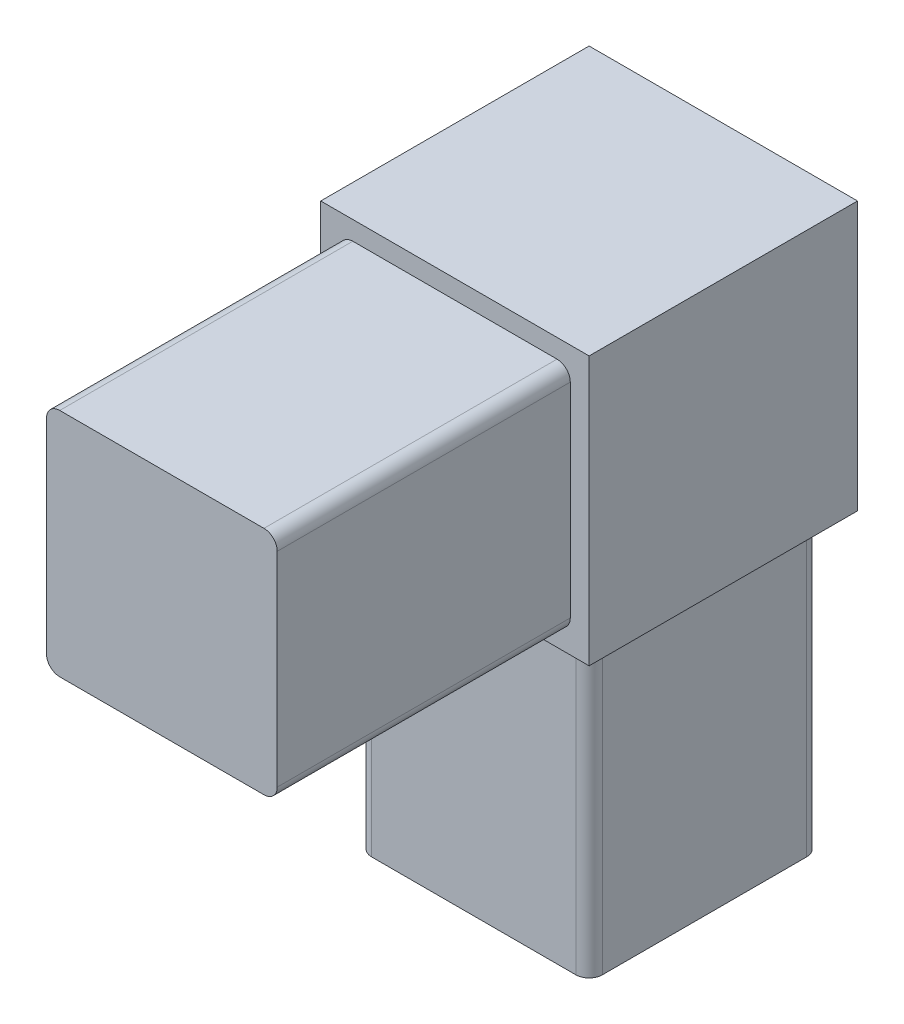
SolidWorks part; units mm, degrees
ref_plane "Front Plane" through (0, 0, 0) normal (0, 0, 1) x (1, 0, 0)
ref_plane "Top Plane" through (0, 0, 0) normal (0, 1, 0) x (1, 0, 0)
ref_plane "Right Plane" through (0, 0, 0) normal (1, 0, 0) x (0, 0, -1)
sketch "Sketch1" plane through (0, 0, 0) normal (0, 1, 0) x (1, 0, 0)
  line L1 (-11.049, 11.049) -> (11.049, 11.049)
  line L2 (-11.049, 11.049) -> (-11.049, -11.049)
  line L3 (-11.049, -11.049) -> (11.049, -11.049)
  line L4 (11.049, 11.049) -> (11.049, -11.049)
  line L5 (-11.049, 11.049) -> (11.049, -11.049) construction
  line L6 (-11.049, -11.049) -> (11.049, 11.049) construction
  point P0 (0, 0)
  dimension "D1" = 22.098
extrude "Boss-Extrude1" add sketch "Sketch1" along normal blind 28.067
sketch "Sketch2" plane through (0, 28.067, 0) normal (0, 1, 0) x (1, 0, 0)
  line L1 (-12.8524, -12.8524) -> (12.8524, -12.8524)
  line L2 (-12.8524, -12.8524) -> (-12.8524, 12.8524)
  line L3 (-12.8524, 12.8524) -> (12.8524, 12.8524)
  line L4 (12.8524, -12.8524) -> (12.8524, 12.8524)
  line L5 (-12.8524, -12.8524) -> (12.8524, 12.8524) construction
  line L6 (-12.8524, 12.8524) -> (12.8524, -12.8524) construction
  point P0 (0, 0)
  dimension "D1" = 25.7048
  dimension "D2" = 25.7048
extrude "Boss-Extrude2" add sketch "Sketch2" along normal blind 25.7048
sketch "Sketch3" plane through (0, 0, 12.8524) normal (0, 0, 1) x (1, 0, 0)
  line L0 (-12.8524, 53.7718) -> (12.8524, 28.067) construction
  line L2 (-11.049, 29.8704) -> (11.049, 29.8704)
  line L3 (-11.049, 29.8704) -> (-11.049, 51.9684)
  line L4 (-11.049, 51.9684) -> (11.049, 51.9684)
  line L5 (11.049, 29.8704) -> (11.049, 51.9684)
  line L6 (-11.049, 29.8704) -> (11.049, 51.9684) construction
  line L7 (-11.049, 51.9684) -> (11.049, 29.8704) construction
  point P4 (0, 40.9194)
  dimension "D1" = 22.098
extrude "Boss-Extrude3" add sketch "Sketch3" along normal blind 28.067
fillet "Fillet1" radius 1.27 8 edges at (11.049, 51.9684, 26.8859) (11.049, 29.8704, 26.8859) (-11.049, 51.9684, 26.8859) (-11.049, 29.8704, 26.8859) (-11.049, 14.0335, 11.049) (11.049, 14.0335, 11.049) (-11.049, 14.0335, -11.049) (11.049, 14.0335, -11.049)
